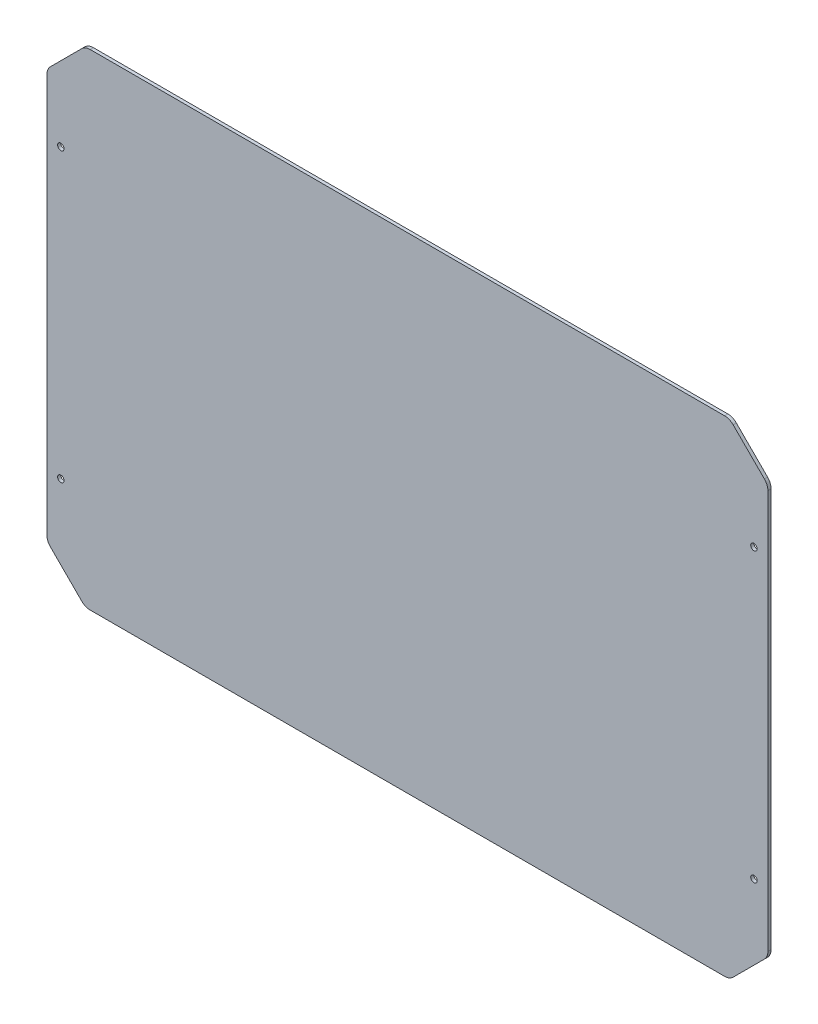
SolidWorks part; units mm, degrees
material "Glass"
ref_plane "Plan de face" through (0, 0, 0) normal (0, 0, 1) x (1, 0, 0)
ref_plane "Plan de dessus" through (0, 0, 0) normal (0, 1, 0) x (1, 0, 0)
ref_plane "Plan de droite" through (0, 0, 0) normal (1, 0, 0) x (0, 0, -1)
sketch "Sketch2" plane through (0, 0, 0) normal (0, 0, 1) x (1, 0, 0)
  line L24 (-451.5, 256) -> (-451.5, -256)
  line L25 (-403.5, -304) -> (403.5, -304)
  line L26 (451.5, 256) -> (451.5, -256)
  line L27 (-403.5, 304) -> (403.5, 304)
  line L28 (-451.5, -256) -> (-403.5, -304)
  line L29 (403.5, -304) -> (451.5, -256)
  line L30 (-403.5, 304) -> (-451.5, 256)
  line L31 (403.5, 304) -> (451.5, 256)
  line L40 (0, 304) -> (0, -304) construction
  line L44 (-434, -180) -> (434, -180) construction
  line L45 (-434, -180) -> (-434, 180) construction
  line L46 (-434, 180) -> (434, 180) construction
  line L47 (434, -180) -> (434, 180) construction
  line L48 (-434, -180) -> (434, 180) construction
  line L49 (-434, 180) -> (434, -180) construction
  circle A1 centre (-434, 180) radius 4.05
  circle A2 centre (-434, -180) radius 4.05
  circle A3 centre (434, -180) radius 4.05
  circle A4 centre (434, 180) radius 4.05
  point P50 (0, 0)
  dimension "D28" = 8.1
  dimension "D3" = 451.5
  dimension "D4" = 17.5
  dimension "D17" = 608
  dimension "D18" = 903
  dimension "D23" = 360
extrude "Boss-Extrude1" add sketch "Sketch2" along normal blind 4
fillet "Fillet1" radius 15 8 edges at (-451.5, -256, 2) (-403.5, -304, 2) (403.5, -304, 2) (451.5, -256, 2) (451.5, 256, 2) (403.5, 304, 2) (-403.5, 304, 2) (-451.5, 256, 2)
